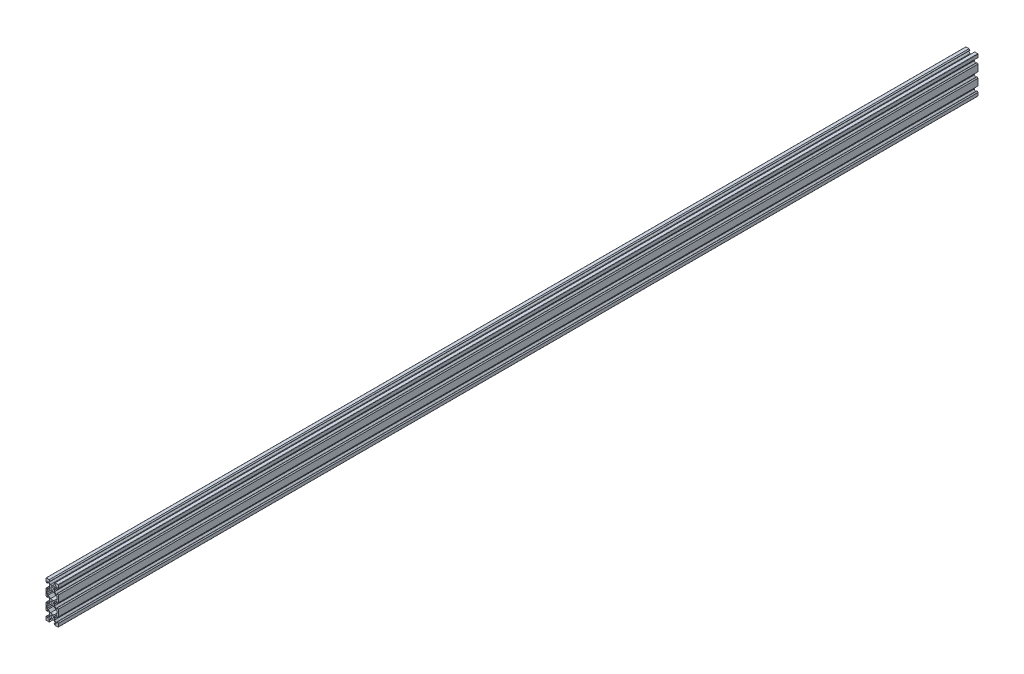
SolidWorks part; units mm, degrees
material "6061-T6 (SS)"
ref_plane "Front Plane" through (0, 0, 0) normal (0, 0, 1) x (1, 0, 0)
ref_plane "Top Plane" through (0, 0, 0) normal (0, 1, 0) x (1, 0, 0)
ref_plane "Right Plane" through (0, 0, 0) normal (1, 0, 0) x (0, 0, -1)
sketch "Sketch1" plane through (0, 0, 0) normal (0, 0, 1) x (1, 0, 0)
  line L0 (0, 0) -> (10, 0) construction
  line L1 (9.5, -30) -> (-9.5, -30)
  line L2 (10, -29.5) -> (10, 29.5)
  line L3 (9.5, 30) -> (-9.5, 30)
  line L4 (-10, -29.5) -> (-10, 29.5)
  line L5 (10, -30) -> (-10, 30) construction
  line L6 (10, 30) -> (-10, -30) construction
  circle A0 centre (0, 20) radius 2.1
  circle A1 centre (0, 0) radius 2.1
  circle A2 centre (0, -20) radius 2.1
  arc A3 (-9.5, -30) -> (-10, -29.5) centre (-9.5, -29.5) cw
  arc A4 (9.5, -30) -> (10, -29.5) centre (9.5, -29.5) ccw
  arc A5 (10, 29.5) -> (9.5, 30) centre (9.5, 29.5) ccw
  arc A6 (-9.5, 30) -> (-10, 29.5) centre (-9.5, 29.5) ccw
  point P0 (0, 0)
  line B0 (0, 20) -> (0, 30) construction
  line B1 (0, 23.69) -> (-0.21, 23.9)
  line B2 (-0.21, 23.9) -> (-2.8393, 23.9)
  line B3 (-2.8393, 23.9) -> (-5.5, 26.5607)
  line B4 (-5.5, 26.5607) -> (-5.5, 28.2)
  line B5 (-5.5, 28.2) -> (-3.125, 28.2)
  line B6 (-3.125, 28.2) -> (-3.125, 28.545)
  line B7 (-3.125, 28.545) -> (-4.58, 30)
  line B8 (-4.58, 30) -> (4.58, 30)
  line B9 (0, 20) -> (-5.9132, 25.9132) construction
  line B10 (3.125, 28.545) -> (4.58, 30)
  line B11 (3.125, 28.2) -> (3.125, 28.545)
  line B12 (5.5, 28.2) -> (3.125, 28.2)
  line B13 (5.5, 26.5607) -> (5.5, 28.2)
  line B14 (2.8393, 23.9) -> (5.5, 26.5607)
  line B15 (0.21, 23.9) -> (2.8393, 23.9)
  line B16 (0, 23.69) -> (0.21, 23.9)
  line B17 (0, 20) -> (-10, 20) construction
  line B18 (-3.69, 20) -> (-3.9, 19.79)
  line B19 (-3.9, 19.79) -> (-3.9, 17.1607)
  line B20 (-3.9, 17.1607) -> (-6.5607, 14.5)
  line B21 (-6.5607, 14.5) -> (-8.2, 14.5)
  line B22 (-8.2, 14.5) -> (-8.2, 16.875)
  line B23 (-8.2, 16.875) -> (-8.545, 16.875)
  line B24 (-8.545, 16.875) -> (-10, 15.42)
  line B25 (-10, 15.42) -> (-10, 24.58)
  line B26 (0, 20) -> (-5.9132, 14.0868) construction
  line B27 (-8.545, 23.125) -> (-10, 24.58)
  line B28 (-8.2, 23.125) -> (-8.545, 23.125)
  line B29 (-8.2, 25.5) -> (-8.2, 23.125)
  line B30 (-6.5607, 25.5) -> (-8.2, 25.5)
  line B31 (-3.9, 22.8393) -> (-6.5607, 25.5)
  line B32 (-3.9, 20.21) -> (-3.9, 22.8393)
  line B33 (-3.69, 20) -> (-3.9, 20.21)
  line B34 (0, 0) -> (-10, 0) construction
  line B35 (-3.69, 0) -> (-3.9, -0.21)
  line B36 (-3.9, -0.21) -> (-3.9, -2.8393)
  line B37 (-3.9, -2.8393) -> (-6.5607, -5.5)
  line B38 (-6.5607, -5.5) -> (-8.2, -5.5)
  line B39 (-8.2, -5.5) -> (-8.2, -3.125)
  line B40 (-8.2, -3.125) -> (-8.545, -3.125)
  line B41 (-8.545, -3.125) -> (-10, -4.58)
  line B42 (-10, -4.58) -> (-10, 4.58)
  line B43 (0, 0) -> (-5.9132, -5.9132) construction
  line B44 (-8.545, 3.125) -> (-10, 4.58)
  line B45 (-8.2, 3.125) -> (-8.545, 3.125)
  line B46 (-8.2, 5.5) -> (-8.2, 3.125)
  line B47 (-6.5607, 5.5) -> (-8.2, 5.5)
  line B48 (-3.9, 2.8393) -> (-6.5607, 5.5)
  line B49 (-3.9, 0.21) -> (-3.9, 2.8393)
  line B50 (-3.69, 0) -> (-3.9, 0.21)
  line B51 (0, -20) -> (-10, -20) construction
  line B52 (-3.69, -20) -> (-3.9, -20.21)
  line B53 (-3.9, -20.21) -> (-3.9, -22.8393)
  line B54 (-3.9, -22.8393) -> (-6.5607, -25.5)
  line B55 (-6.5607, -25.5) -> (-8.2, -25.5)
  line B56 (-8.2, -25.5) -> (-8.2, -23.125)
  line B57 (-8.2, -23.125) -> (-8.545, -23.125)
  line B58 (-8.545, -23.125) -> (-10, -24.58)
  line B59 (-10, -24.58) -> (-10, -15.42)
  line B60 (0, -20) -> (-5.9132, -25.9132) construction
  line B61 (-8.545, -16.875) -> (-10, -15.42)
  line B62 (-8.2, -16.875) -> (-8.545, -16.875)
  line B63 (-8.2, -14.5) -> (-8.2, -16.875)
  line B64 (-6.5607, -14.5) -> (-8.2, -14.5)
  line B65 (-3.9, -17.1607) -> (-6.5607, -14.5)
  line B66 (-3.9, -19.79) -> (-3.9, -17.1607)
  line B67 (-3.69, -20) -> (-3.9, -19.79)
  line B68 (0, -20) -> (0, -30) construction
  line B69 (0, -23.69) -> (0.21, -23.9)
  line B70 (0.21, -23.9) -> (2.8393, -23.9)
  line B71 (2.8393, -23.9) -> (5.5, -26.5607)
  line B72 (5.5, -26.5607) -> (5.5, -28.2)
  line B73 (5.5, -28.2) -> (3.125, -28.2)
  line B74 (3.125, -28.2) -> (3.125, -28.545)
  line B75 (3.125, -28.545) -> (4.58, -30)
  line B76 (4.58, -30) -> (-4.58, -30)
  line B77 (0, -20) -> (5.9132, -25.9132) construction
  line B78 (-3.125, -28.545) -> (-4.58, -30)
  line B79 (-3.125, -28.2) -> (-3.125, -28.545)
  line B80 (-5.5, -28.2) -> (-3.125, -28.2)
  line B81 (-5.5, -26.5607) -> (-5.5, -28.2)
  line B82 (-2.8393, -23.9) -> (-5.5, -26.5607)
  line B83 (-0.21, -23.9) -> (-2.8393, -23.9)
  line B84 (0, -23.69) -> (-0.21, -23.9)
  line B85 (0, -20) -> (10, -20) construction
  line B86 (3.69, -20) -> (3.9, -19.79)
  line B87 (3.9, -19.79) -> (3.9, -17.1607)
  line B88 (3.9, -17.1607) -> (6.5607, -14.5)
  line B89 (6.5607, -14.5) -> (8.2, -14.5)
  line B90 (8.2, -14.5) -> (8.2, -16.875)
  line B91 (8.2, -16.875) -> (8.545, -16.875)
  line B92 (8.545, -16.875) -> (10, -15.42)
  line B93 (10, -15.42) -> (10, -24.58)
  line B94 (0, -20) -> (5.9132, -14.0868) construction
  line B95 (8.545, -23.125) -> (10, -24.58)
  line B96 (8.2, -23.125) -> (8.545, -23.125)
  line B97 (8.2, -25.5) -> (8.2, -23.125)
  line B98 (6.5607, -25.5) -> (8.2, -25.5)
  line B99 (3.9, -22.8393) -> (6.5607, -25.5)
  line B100 (3.9, -20.21) -> (3.9, -22.8393)
  line B101 (3.69, -20) -> (3.9, -20.21)
  line B102 (0, 0) -> (10, 0) construction
  line B103 (3.69, 0) -> (3.9, 0.21)
  line B104 (3.9, 0.21) -> (3.9, 2.8393)
  line B105 (3.9, 2.8393) -> (6.5607, 5.5)
  line B106 (6.5607, 5.5) -> (8.2, 5.5)
  line B107 (8.2, 5.5) -> (8.2, 3.125)
  line B108 (8.2, 3.125) -> (8.545, 3.125)
  line B109 (8.545, 3.125) -> (10, 4.58)
  line B110 (10, 4.58) -> (10, -4.58)
  line B111 (0, 0) -> (5.9132, 5.9132) construction
  line B112 (8.545, -3.125) -> (10, -4.58)
  line B113 (8.2, -3.125) -> (8.545, -3.125)
  line B114 (8.2, -5.5) -> (8.2, -3.125)
  line B115 (6.5607, -5.5) -> (8.2, -5.5)
  line B116 (3.9, -2.8393) -> (6.5607, -5.5)
  line B117 (3.9, -0.21) -> (3.9, -2.8393)
  line B118 (3.69, 0) -> (3.9, -0.21)
  line B119 (0, 20) -> (10, 20) construction
  line B120 (3.69, 20) -> (3.9, 20.21)
  line B121 (3.9, 20.21) -> (3.9, 22.8393)
  line B122 (3.9, 22.8393) -> (6.5607, 25.5)
  line B123 (6.5607, 25.5) -> (8.2, 25.5)
  line B124 (8.2, 25.5) -> (8.2, 23.125)
  line B125 (8.2, 23.125) -> (8.545, 23.125)
  line B126 (8.545, 23.125) -> (10, 24.58)
  line B127 (10, 24.58) -> (10, 15.42)
  line B128 (0, 20) -> (5.9132, 25.9132) construction
  line B129 (8.545, 16.875) -> (10, 15.42)
  line B130 (8.2, 16.875) -> (8.545, 16.875)
  line B131 (8.2, 14.5) -> (8.2, 16.875)
  line B132 (6.5607, 14.5) -> (8.2, 14.5)
  line B133 (3.9, 17.1607) -> (6.5607, 14.5)
  line B134 (3.9, 19.79) -> (3.9, 17.1607)
  line B135 (3.69, 20) -> (3.9, 19.79)
  line B136 (-8.2, 7.3) -> (-8.2, 12.7)
  line B137 (-8.2, 12.7) -> (-6.2393, 12.7)
  line B138 (-6.2393, 12.7) -> (-2.8393, 16.1)
  line B139 (-2.8393, 16.1) -> (2.8393, 16.1)
  line B140 (0, 16.1) -> (0, 10) construction
  line B141 (0, 10) -> (-8.2, 10) construction
  line B142 (6.2393, 12.7) -> (2.8393, 16.1)
  line B143 (8.2, 12.7) -> (6.2393, 12.7)
  line B144 (8.2, 7.3) -> (8.2, 12.7)
  line B145 (8.2, 7.3) -> (6.2393, 7.3)
  line B146 (6.2393, 7.3) -> (2.8393, 3.9)
  line B147 (-2.8393, 3.9) -> (2.8393, 3.9)
  line B148 (-6.2393, 7.3) -> (-2.8393, 3.9)
  line B149 (-8.2, 7.3) -> (-6.2393, 7.3)
  line B150 (0, 16.1) -> (0, 20) construction
  line B151 (0, 20) -> (-5.0927, 14.9073) construction
  line B152 (-8.2, -12.7) -> (-8.2, -7.3)
  line B153 (-8.2, -7.3) -> (-6.2393, -7.3)
  line B154 (-6.2393, -7.3) -> (-2.8393, -3.9)
  line B155 (-2.8393, -3.9) -> (2.8393, -3.9)
  line B156 (0, -3.9) -> (0, -10) construction
  line B157 (0, -10) -> (-8.2, -10) construction
  line B158 (6.2393, -7.3) -> (2.8393, -3.9)
  line B159 (8.2, -7.3) -> (6.2393, -7.3)
  line B160 (8.2, -12.7) -> (8.2, -7.3)
  line B161 (8.2, -12.7) -> (6.2393, -12.7)
  line B162 (6.2393, -12.7) -> (2.8393, -16.1)
  line B163 (-2.8393, -16.1) -> (2.8393, -16.1)
  line B164 (-6.2393, -12.7) -> (-2.8393, -16.1)
  line B165 (-8.2, -12.7) -> (-6.2393, -12.7)
  line B166 (0, -3.9) -> (0, 0) construction
  line B167 (0, 0) -> (-5.0927, -5.0927) construction
  dimension "D3" = 4.2
  dimension "D5" = 0.5
  dimension "D1" = 20
  dimension "D2" = 60
  dimension "D4" = 40
sketch_block_instance "V Slot 1-4"
sketch_block "V Slot 1" parameters "D1"=10, "D2"=11, "D3"=4.3, "D4"=1.8, "D5"=0.21, "D6"=45, "D7"=9.16, "D8"=1.5, "D9"=6.25
sketch_block_instance "V Slot 1-5"
sketch_block_instance "V Slot 1-6"
sketch_block_instance "V Slot 1-7"
sketch_block_instance "V Slot 1-8"
sketch_block_instance "V Slot 1-9"
sketch_block_instance "V Slot 1-10"
sketch_block_instance "V Slot 1-11"
sketch_block_instance "Center Cutout 1-1"
sketch_block "Center Cutout 1" parameters "D1"=5.4, "D2"=12.2, "D3"=8.2, "D4"=45, "D5"=10, "D6"=1.5
sketch_block_instance "Center Cutout 1-2"
extrude "Boss-Extrude1" add sketch "Sketch1" along normal blind 1500 contours B135 B120 B121 B122 B123 B124 B125 B126 L2 A5 L3 B10 B11 B12 B13 B14 B15 B16 B1 B2 B3 B4 B5 B6 B7 A6 L4 B27 B28 B29 B30 B31 B32 B33 B18 B19 B20 B21 B22 B23 B24 B44 B45 B46 B47 B48 B49 B50 B35
